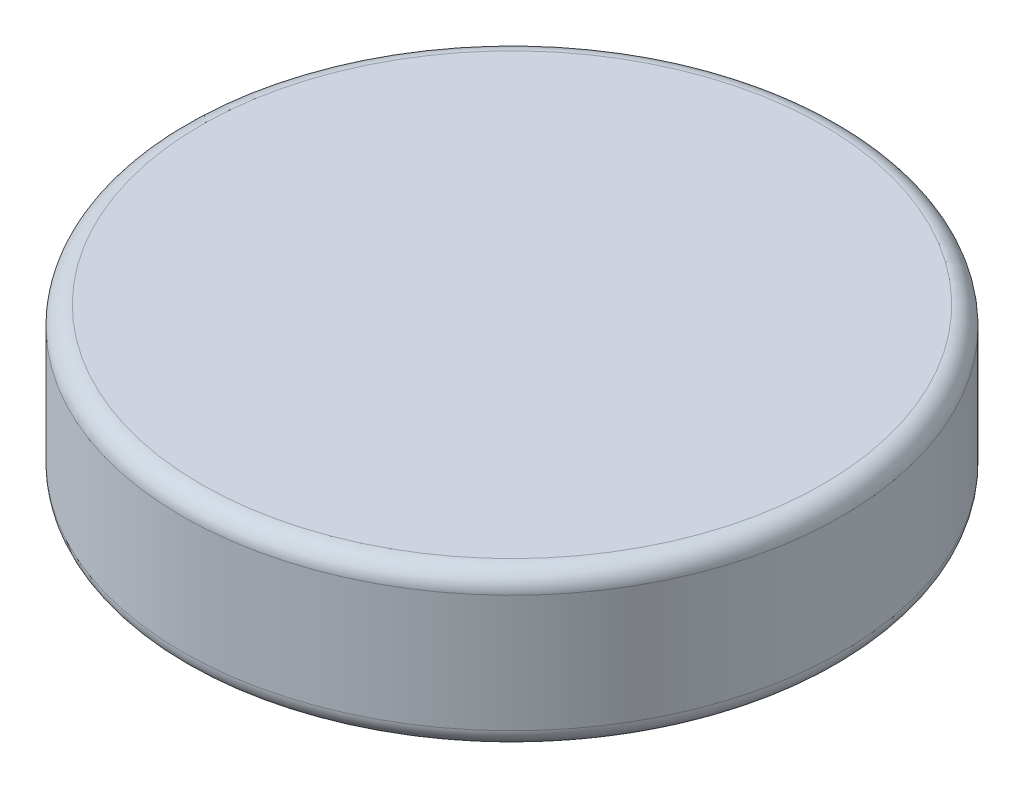
SolidWorks part; units mm, degrees
ref_plane "Front Plane" through (0, 0, 0) normal (0, 0, 1) x (1, 0, 0)
ref_plane "Top Plane" through (0, 0, 0) normal (0, 1, 0) x (1, 0, 0)
ref_plane "Right Plane" through (0, 0, 0) normal (1, 0, 0) x (0, 0, -1)
sketch "Sketch1" plane through (0, 0, 0) normal (0, 1, 0) x (1, 0, 0)
  circle A0 centre (0, 0) radius 177
extrude "Boss-Extrude1" add sketch "Sketch1" along normal blind 83
fillet "Fillet1" radius 10 2 edges at (0, 0, 177) (0, 83, 177)
sketch "Sketch2" plane through (0, 0, 0) normal (0, -1, 0) x (1, 0, 0)
  circle A0 centre (0, 0) radius 143.2602
extrude "Boss-Extrude2" add sketch "Sketch2" along normal blind 15
